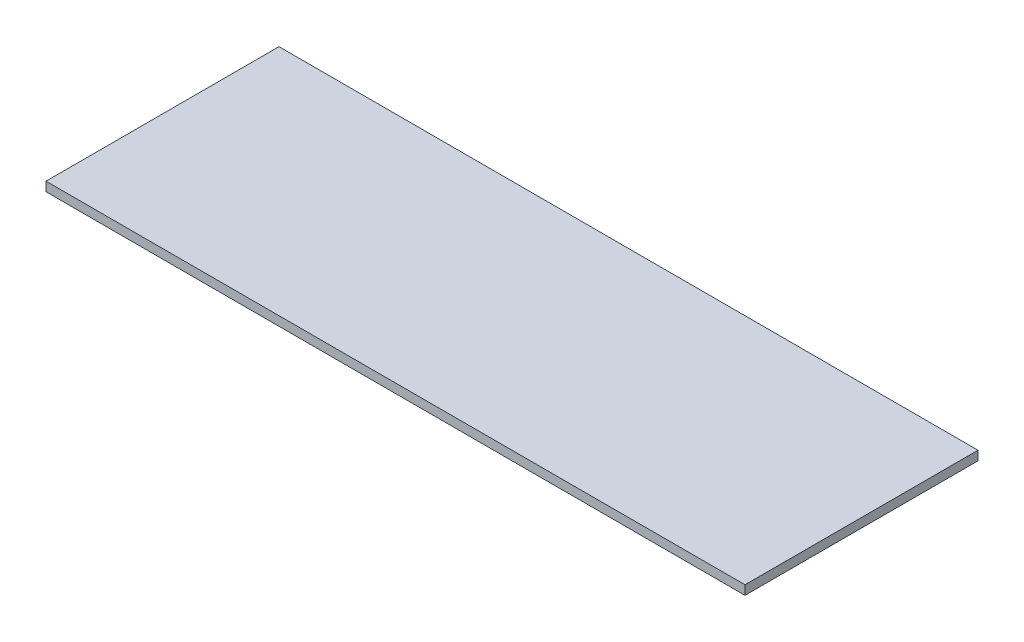
SolidWorks part; units mm, degrees
ref_plane "Front Plane" through (0, 0, 0) normal (0, 0, 1) x (1, 0, 0)
ref_plane "Top Plane" through (0, 0, 0) normal (0, 1, 0) x (1, 0, 0)
ref_plane "Right Plane" through (0, 0, 0) normal (1, 0, 0) x (0, 0, -1)
sketch "Sketch1" plane through (0, 0, 0) normal (0, 1, 0) x (1, 0, 0)
  line L2 (-38.1, 12.7) -> (38.1, 12.7)
  line L3 (-38.1, 12.7) -> (-38.1, -12.7)
  line L4 (-38.1, -12.7) -> (38.1, -12.7)
  line L5 (38.1, 12.7) -> (38.1, -12.7)
  line L6 (-38.1, 12.7) -> (38.1, -12.7) construction
  line L7 (-38.1, -12.7) -> (38.1, 12.7) construction
  point P2 (0, 0)
  dimension "D1" = 76.2
  dimension "D2" = 25.4
extrude "Boss-Extrude1" add sketch "Sketch1" along normal blind 1
